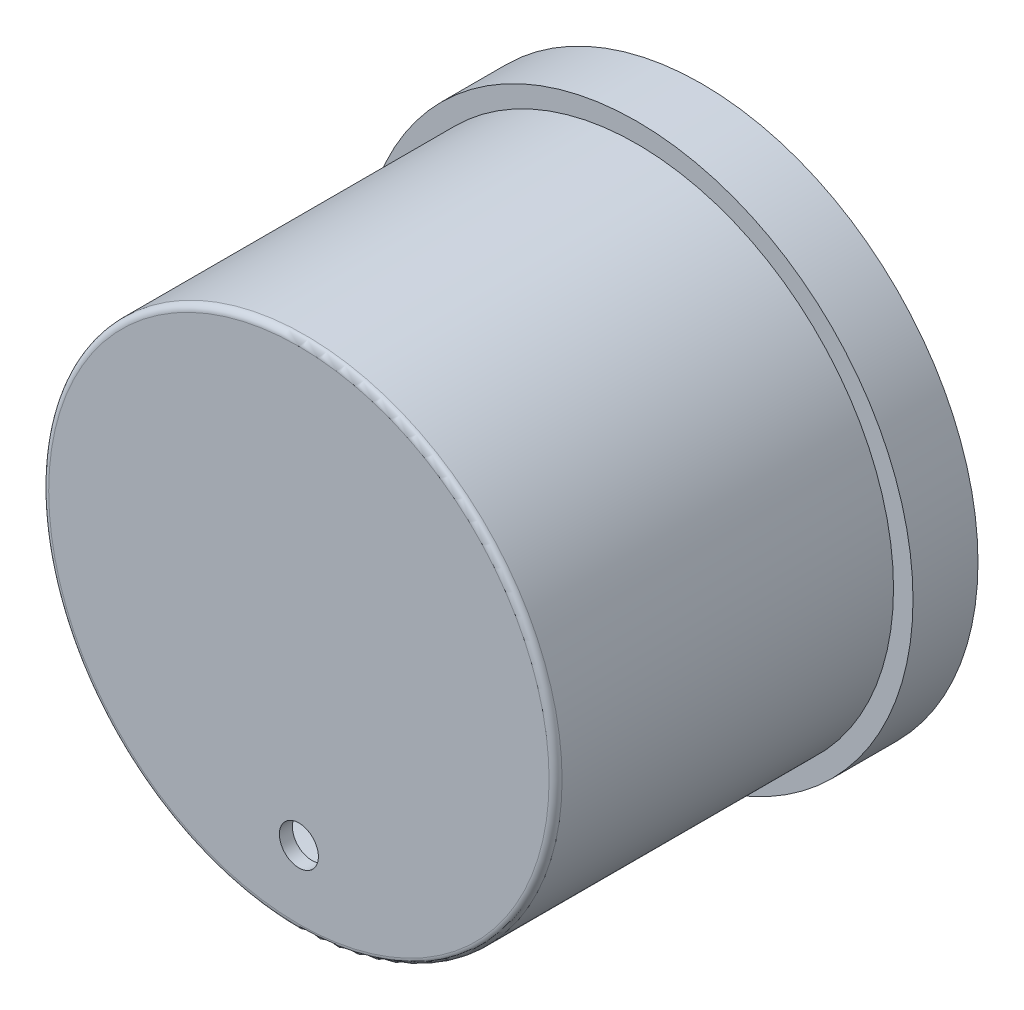
SolidWorks part; units mm, degrees
material "PVC Rigid"
ref_plane "Front Plane" through (0, 0, 0) normal (0, 0, 1) x (1, 0, 0)
ref_plane "Top Plane" through (0, 0, 0) normal (0, 1, 0) x (1, 0, 0)
ref_plane "Right Plane" through (0, 0, 0) normal (1, 0, 0) x (0, 0, -1)
sketch "Sketch1" plane through (0, 0, 0) normal (0, 0, 1) x (1, 0, 0)
  circle A0 centre (0, 0) radius 37.5
  circle A1 centre (0, 0) radius 42.5
  dimension "D1" = 75
  dimension "D2" = 5
extrude "Boss-Extrude1" add sketch "Sketch1" along normal blind 10
sketch "Sketch2" plane through (0, 0, 10) normal (0, 0, 1) x (1, 0, 0)
  circle A0 centre (0, 0) radius 37.5
  circle A1 centre (0, 0) radius 39.5
  circle A5 centre (0, 0) radius 37.5 construction
  dimension "D1" = 2
extrude "Boss-Extrude2" add sketch "Sketch2" along normal blind 50
sketch "Sketch3" plane through (0, 0, 60) normal (0, 0, 1) x (1, 0, 0)
  circle A0 centre (0, 0) radius 39.5
  circle A1 centre (0, 0) radius 39.5 construction
extrude "Boss-Extrude3" add sketch "Sketch3" along normal blind 2
fillet "Fillet1" radius 1 1 edges at (39.5, 0, 62)
sketch "Sketch4" plane through (0, 0, 62) normal (0, 0, 1) x (1, 0, 0)
  line L0 (0, -42.5) -> (0, -39.5)
  line L1 (0, -39.5) -> (0, -50.0041)
  line L2 (0, -50.0041) -> (0, -48.0041)
  line L3 (0, -48.0041) -> (0, -8.0041)
  circle A0 centre (0, 0) radius 42.5 construction
  circle A1 centre (0, 0) radius 39.5 construction
  circle A2 centre (0, -28.0041) radius 3
  dimension "D3" = 6
  dimension "D1" = 2
  dimension "D2" = 40
extrude "Cut-Extrude1" cut sketch "Sketch4" against normal blind 100 contours L3 A2 | L3 A2
